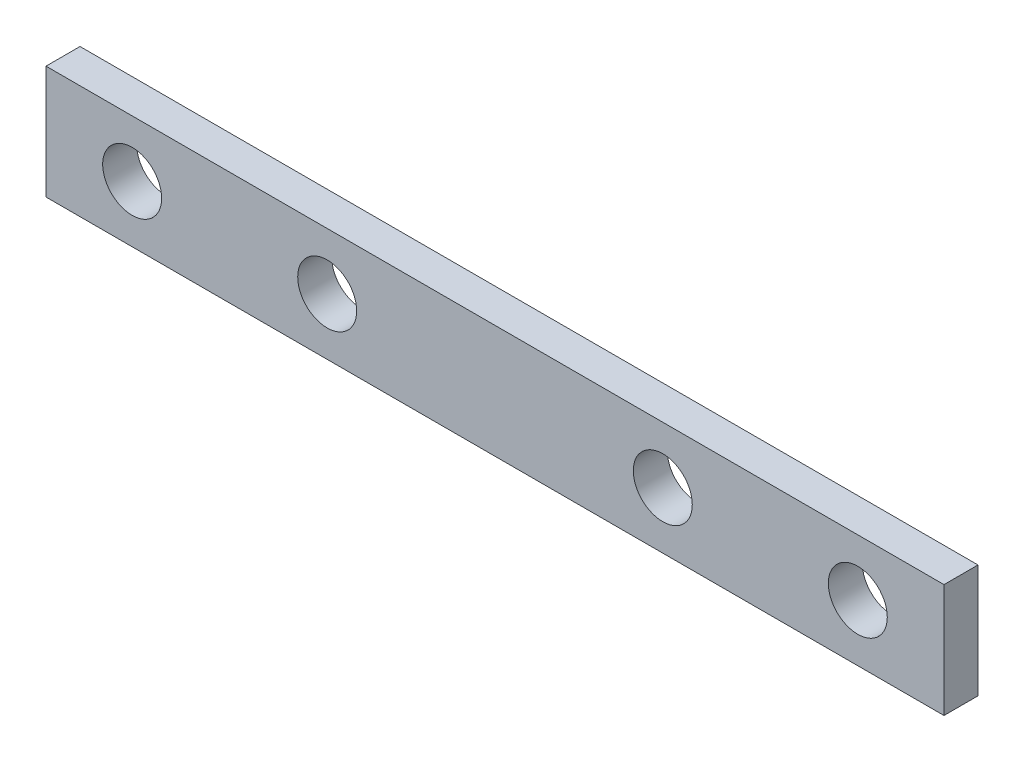
SolidWorks part; units mm, degrees
ref_plane "Front Plane" through (0, 0, 0) normal (0, 0, 1) x (1, 0, 0)
ref_plane "Top Plane" through (0, 0, 0) normal (0, 1, 0) x (1, 0, 0)
ref_plane "Right Plane" through (0, 0, 0) normal (1, 0, 0) x (0, 0, -1)
sketch "Sketch1" plane through (0, 0, 0) normal (0, 0, 1) x (1, 0, 0)
  line L1 (-60.27, -12.0406) -> (40.314, -12.0406)
  line L2 (-60.27, -12.0406) -> (-60.27, -24.7406)
  line L3 (-60.27, -24.7406) -> (40.314, -24.7406)
  line L4 (40.314, -12.0406) -> (40.314, -24.7406)
  circle A0 centre (30.662, -18.3906) radius 3.302
  circle A2 centre (-50.618, -18.3906) radius 3.302
  dimension "D3" = 6.604
  dimension "D5" = 6.604
  dimension "D1" = 100.584
  dimension "D2" = 12.7
  dimension "D7" = 6.35
  dimension "D9" = 9.652
  dimension "D12" = 6.35
  dimension "D13" = 9.652
extrude "Boss-Extrude2" add sketch "Sketch1" along normal blind 3.81
sketch "Sketch2" plane through (0, 0, 0) normal (0, 0, -1) x (-1, 0, 0)
  line L0 (60.27, -24.7406) -> (-40.314, -24.7406) construction
  line L1 (36.648, -24.7406) -> (-16.692, -24.7406)
  line L2 (36.648, -24.7406) -> (36.648, -12.0406)
  line L3 (36.648, -12.0406) -> (-16.692, -12.0406)
  line L4 (-16.692, -24.7406) -> (-16.692, -12.0406)
  line L5 (-40.314, -12.0406) -> (60.27, -12.0406) construction
  circle A0 centre (50.618, -18.3906) radius 3.302 construction
  circle A1 centre (-30.662, -18.3906) radius 3.302 construction
  circle A2 centre (28.774, -18.3906) radius 3.302
  circle A3 centre (-8.818, -18.3906) radius 3.302
  dimension "D4" = 6.604
  dimension "D5" = 6.604
  dimension "D1" = 53.34
  dimension "D2" = 13.97
  dimension "D3" = 13.97
  dimension "D6" = 6.35
  dimension "D7" = 6.35
  dimension "D8" = 7.874
  dimension "D9" = 7.874
extrude "Cut-Extrude1" cut sketch "Sketch2" against normal up to next contours A3 | A2
